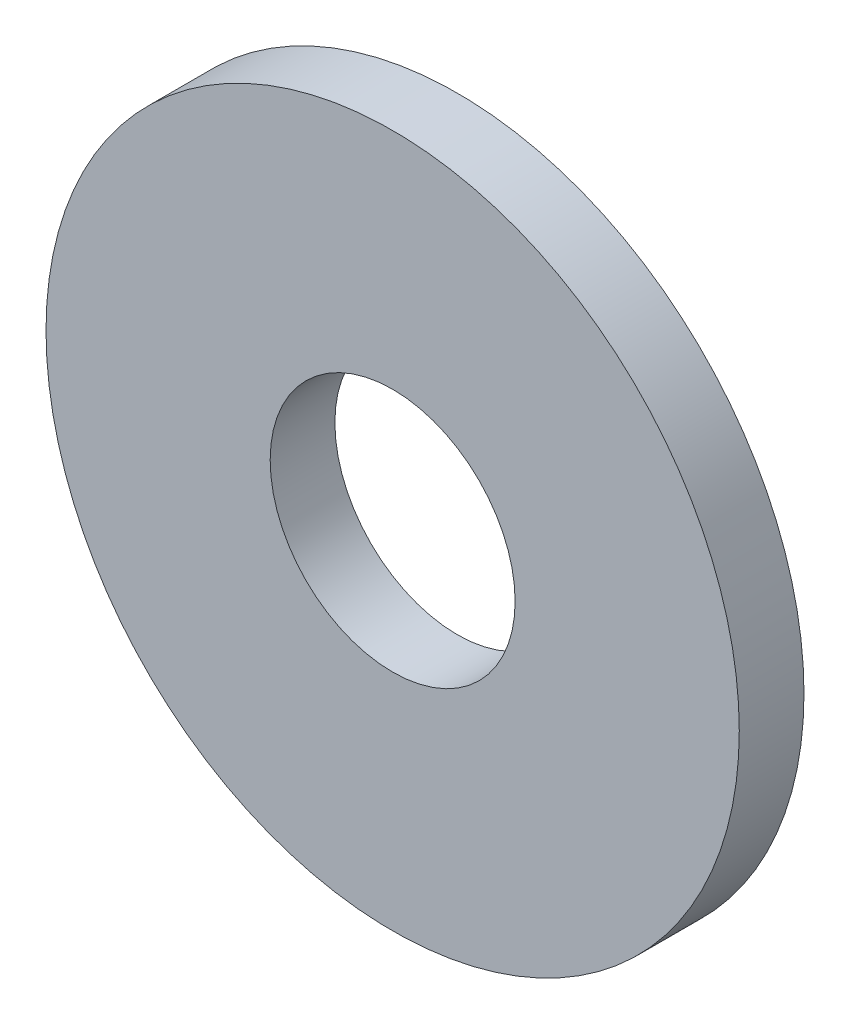
SolidWorks part; units mm, degrees
ref_plane "Front Plane" through (0, 0, 0) normal (0, 0, 1) x (1, 0, 0)
ref_plane "Top Plane" through (0, 0, 0) normal (0, 1, 0) x (1, 0, 0)
ref_plane "Right Plane" through (0, 0, 0) normal (1, 0, 0) x (0, 0, -1)
sketch "Sketch1" plane through (0, 0, 0) normal (0, 0, 1) x (1, 0, 0)
  circle A0 centre (0, 0) radius 7.5
  circle A1 centre (0, 0) radius 2.65
  dimension "OD" = 15
  dimension "ID1" = 5.3
extrude "Boss-Extrude1" add sketch "Sketch1" along normal blind 1.4
